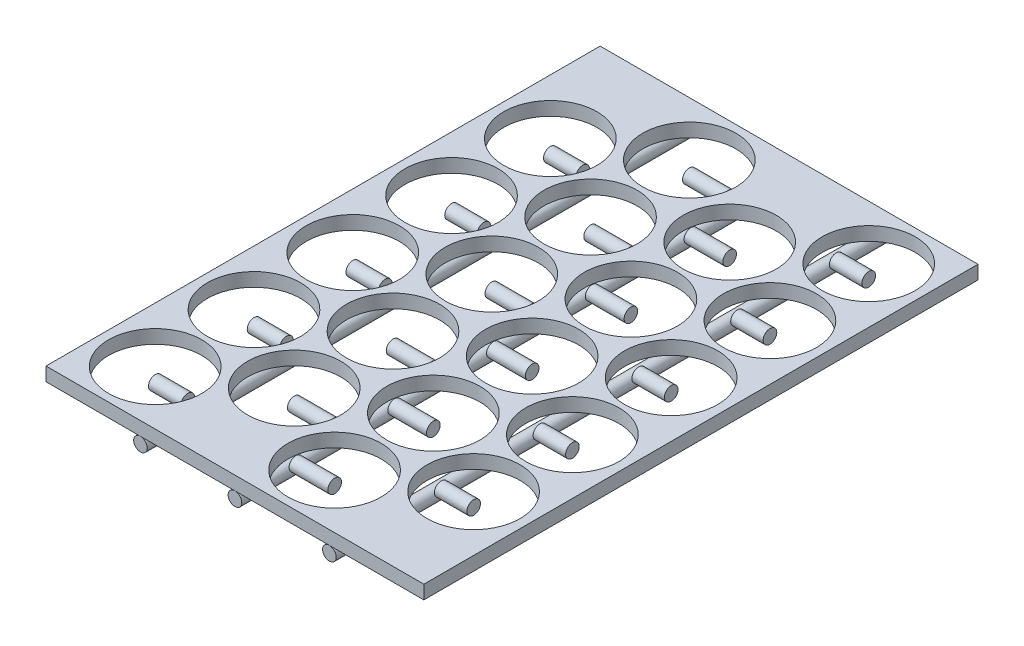
SolidWorks part; units mm, degrees
ref_plane "Front Plane" through (0, 0, 0) normal (0, 0, 1) x (1, 0, 0)
ref_plane "Top Plane" through (0, 0, 0) normal (0, 1, 0) x (1, 0, 0)
ref_plane "Right Plane" through (0, 0, 0) normal (1, 0, 0) x (0, 0, -1)
sketch "Sketch1" plane through (0, 0, 0) normal (0, 1, 0) x (1, 0, 0)
  line L0 (-9.15, 64.525) -> (-9.15, 32.2746) construction
  line L1 (-22, -64.525) -> (66, -64.525)
  line L2 (-22, -64.525) -> (-22, 64.525)
  line L3 (-22, 64.525) -> (66, 64.525)
  line L4 (22, -64.525) -> (22, 64.525) construction
  line L5 (-22, -64.525) -> (22, 64.525) construction
  line L6 (-22, 64.525) -> (22, -64.525) construction
  line L7 (-9.15, 40.075) -> (26.1125, 40.075) construction
  line L8 (-9.15, 40.075) -> (11.3748, 51.925) construction
  line L9 (66, -64.525) -> (66, 64.525)
  circle A2 centre (11.3748, 51.925) radius 10.85
  circle A3 centre (-9.15, 40.075) radius 10.85
  circle A4 centre (-9.1548, 17.075) radius 10.85
  circle A5 centre (11.37, 28.925) radius 10.85
  circle A6 centre (-9.1596, -5.925) radius 10.85
  circle A7 centre (11.3652, 5.925) radius 10.85
  circle A8 centre (-9.1644, -28.925) radius 10.85
  circle A9 centre (11.3604, -17.075) radius 10.85
  circle A10 centre (-9.1692, -51.925) radius 10.85
  circle A11 centre (11.3556, -40.075) radius 10.85
  circle A12 centre (53.15, 51.925) radius 10.85
  circle A13 centre (32.6252, 40.075) radius 10.85
  circle A14 centre (53.1452, 28.925) radius 10.85
  circle A15 centre (32.6204, 17.075) radius 10.85
  circle A16 centre (53.1404, 5.925) radius 10.85
  circle A17 centre (32.6156, -5.925) radius 10.85
  circle A18 centre (53.1356, -17.075) radius 10.85
  circle A19 centre (32.6108, -28.925) radius 10.85
  circle A20 centre (53.1308, -40.075) radius 10.85
  circle A21 centre (32.606, -51.925) radius 10.85
  point P0 (0, 0)
  dimension "D3" = 21.7
  dimension "D4" = 21.7
  dimension "D5" = 2
  dimension "D6" = 60
  dimension "D7" = 5
  dimension "D8" = 1.75
  dimension "D9" = 2
  dimension "D10" = 2
  dimension "D2" = 1.75
  dimension "D11" = 2
  dimension "D1" = 44
extrude "Boss-Extrude2" add sketch "Sketch1" along normal blind 3.175 contours L3 L4 L1 L2
sketch "Sketch2" plane through (0, 0, 64.525) normal (0, 0, 1) x (1, 0, 0)
  line L5 (-22, 0) -> (66, 0) construction
  circle A0 centre (0, -1.5875) radius 1.5875
  dimension "D1" = 3.175
extrude "Boss-Extrude3" add sketch "Sketch2" against normal up to surface (129.05 mm away) separate body up to face at (22, 1.5875, -64.525)
ref_plane "Mid Plane" through (22, 0, 0) normal (1, 0, 0) x (0, 0, -1)
sketch "Sketch7" plane through (0, 0, 0) normal (0, 1, 0) x (1, 0, 0)
  line L0 (-9.15, 40.075) -> (-1.5875, 40.075)
  line L1 (-1.5875, 64.525) -> (-1.5875, -64.525) construction
  line L2 (-1.5875, 40.075) -> (-1.5875, 41.6625)
  line L3 (-1.5875, 41.6625) -> (-9.15, 41.6625)
  line L4 (-9.15, 41.6625) -> (-9.15, 40.075)
  dimension "D1" = 1.5875
revolve "Revolve4" add sketch "Sketch7" angle 360 about L0
pattern_linear "LPattern2" count 5 spacing 23 along (0, 0, 1) of bodies 116
sketch "Sketch9" plane through (0, 0, 64.525) normal (0, 0, 1) x (1, 0, 0)
  line L1 (22, -1.7463) -> (22, 1.7463) construction
  line L2 (-22, 0) -> (66, 0) construction
  circle A1 centre (44, -1.5875) radius 1.5875
  dimension "D1" = 3.175
  dimension "D2" = 22
extrude "Boss-Extrude4" add sketch "Sketch9" against normal up to surface (129.05 mm away) separate body up to face at (22, 1.5875, -64.525)
sketch "Sketch10" plane through (0, 0, 0) normal (0, 1, 0) x (1, 0, 0)
  line L0 (53.15, 51.925) -> (45.5875, 51.925)
  line L1 (45.5875, -64.525) -> (45.5875, 64.525) construction
  line L2 (45.5875, 51.925) -> (45.5875, 53.5125)
  line L3 (45.5875, 53.5125) -> (53.15, 53.5125)
  line L4 (53.15, 53.5125) -> (53.15, 51.925)
  dimension "D1" = 1.5875
revolve "Revolve5" add sketch "Sketch10" angle 360 about L0
pattern_linear "LPattern3" count 5 spacing 23 along (0, 0, 1) of bodies 148
sketch "Sketch11" plane through (0, 0, 64.525) normal (0, 0, 1) x (1, 0, 0)
  line L2 (22, -1.7463) -> (22, 1.7463) construction
  line L3 (-22, 0) -> (66, 0) construction
  circle A0 centre (22, -1.5875) radius 1.5875
  dimension "D1" = 3.175
extrude "Boss-Extrude5" add sketch "Sketch11" against normal up to surface (129.05 mm away) separate body up to face at (22, 1.5875, -64.525)
sketch "Sketch12" plane through (0, 0, 0) normal (0, 1, 0) x (1, 0, 0)
  line L0 (11.3748, 51.925) -> (20.4125, 51.925)
  line L1 (20.4125, 64.525) -> (20.4125, -64.525) construction
  line L2 (20.4125, 51.925) -> (20.4125, 53.5125)
  line L3 (20.4125, 53.5125) -> (11.3748, 53.5125)
  line L4 (11.3748, 53.5125) -> (11.3748, 51.925)
  dimension "D1" = 1.5875
revolve "Revolve6" add sketch "Sketch12" angle 360 about L0
pattern_linear "LPattern4" count 5 spacing 23 along (0, 0, 1) of bodies 154
sketch "Sketch13" plane through (0, 0, 0) normal (0, 1, 0) x (1, 0, 0)
  line L0 (32.6252, 40.075) -> (23.5875, 40.075)
  line L1 (23.5875, -64.525) -> (23.5875, 64.525) construction
  line L2 (23.5875, 40.075) -> (23.5875, 41.6625)
  line L3 (23.5875, 41.6625) -> (32.6252, 41.6625)
  line L4 (32.6252, 41.6625) -> (32.6252, 40.075)
  dimension "D1" = 1.5875
revolve "Revolve7" add sketch "Sketch13" angle 360 about L0
pattern_linear "LPattern5" count 5 spacing 23 along (0, 0, 1) of bodies 159
